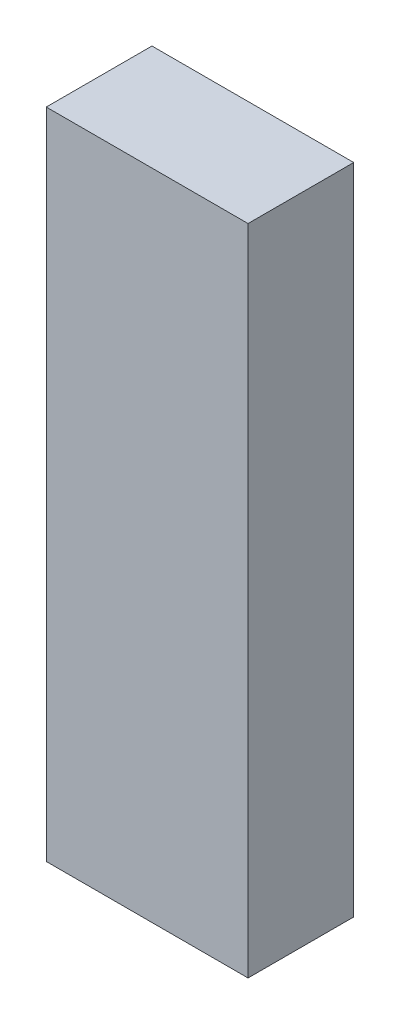
SolidWorks part; units mm, degrees
ref_plane "Front Plane" through (0, 0, 0) normal (0, 0, 1) x (1, 0, 0)
ref_plane "Top Plane" through (0, 0, 0) normal (0, 1, 0) x (1, 0, 0)
ref_plane "Right Plane" through (0, 0, 0) normal (1, 0, 0) x (0, 0, -1)
sketch "Sketch1" plane through (0, 0, 0) normal (0, 1, 0) x (1, 0, 0)
  line L1 (-21, -11) -> (21, -11)
  line L2 (-21, -11) -> (-21, 11)
  line L3 (-21, 11) -> (21, 11)
  line L4 (21, -11) -> (21, 11)
  line L5 (-21, -11) -> (21, 11) construction
  line L6 (-21, 11) -> (21, -11) construction
  point P1 (0, 0)
  dimension "D1" = 22
  dimension "D2" = 42
extrude "Boss-Extrude1" add sketch "Sketch1" along normal blind 136
